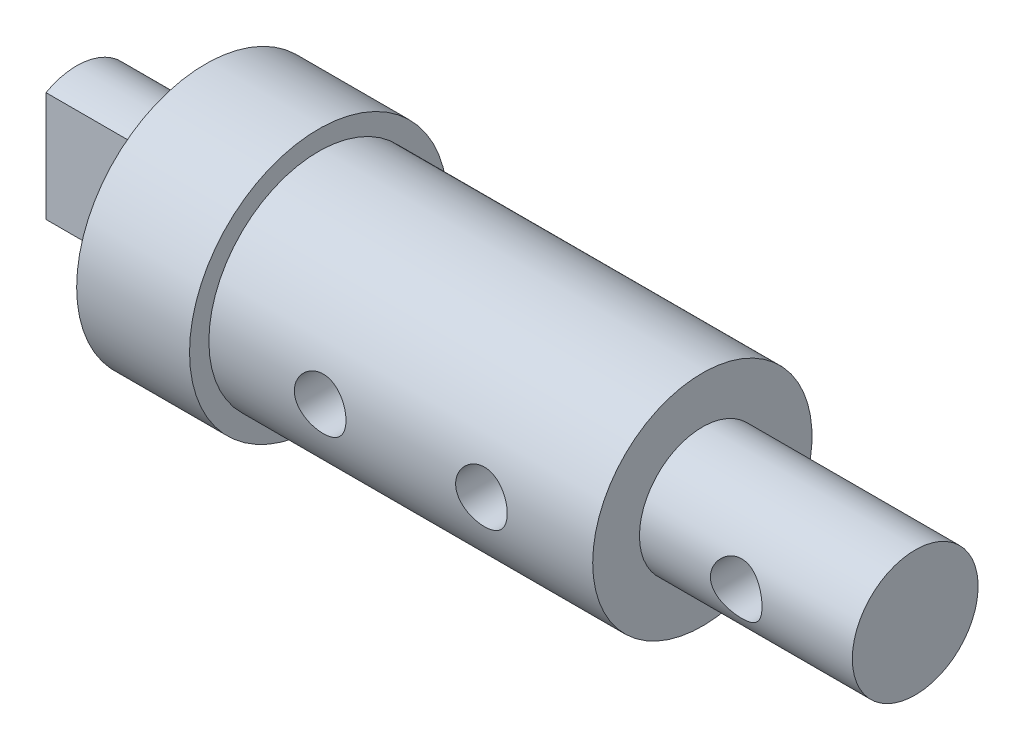
SolidWorks part; units mm, degrees
material "Nylon 101"
ref_plane "Front Plane" through (0, 0, 0) normal (0, 0, 1) x (1, 0, 0)
ref_plane "Top Plane" through (0, 0, 0) normal (0, 1, 0) x (1, 0, 0)
ref_plane "Right Plane" through (0, 0, 0) normal (1, 0, 0) x (0, 0, -1)
sketch "Sketch1" plane through (0, 0, 0) normal (0, 0, 1) x (1, 0, 0)
  line L0 (-11, 0) -> (11, 0)
  line L1 (11, 0) -> (11, 1.95)
  line L2 (11, 1.95) -> (4.4, 1.95)
  line L3 (4.4, 1.95) -> (4.4, 3.4)
  line L4 (0, 0) -> (49607.6871, 0) construction
  line L5 (4.4, 3.4) -> (-7.5, 3.4)
  line L6 (-7.5, 3.4) -> (-7.5, 4)
  line L7 (-7.5, 4) -> (-11, 4)
  line L8 (-11, 4) -> (-11, 0)
  point P4 (0, 0)
  dimension "D1" = 6.8
  dimension "D2" = 3.9
  dimension "D3" = 6.6
  dimension "D4" = 3.5
  dimension "D5" = 22
  dimension "D6" = 8
revolve "Revolve1" add sketch "Sketch1" angle 360 about L4
ref_plane "Plane1" through (0, 0, 3.4) normal (0, 0, 1) x (1, 0, 0)
sketch "Sketch2" plane through (0, 0, 3.4) normal (0, 0, 1) x (1, 0, 0)
  line L0 (-7.5, 0) -> (-4.05, 0) construction
  line L1 (-4.05, 0) -> (0.95, 0) construction
  line L2 (0.95, 0) -> (4.4, 0) construction
  line L3 (4.4, -3.4) -> (4.4, 3.4) construction
  line L4 (-7.5, -3.4) -> (-7.5, 3.4) construction
  dimension "D1" = 5
hole_wizard "M2x0.4 Tapped Hole1" positions "Sketch3" profile "Sketch5" tap size "M2x0.4" standard "ANSI Metric" end condition through all
sketch "Sketch3" plane through (0, 0, 3.4) normal (0, 0, 1) x (1, 0, 0)
  point P0 (-4.05, 0)
  point P3 (0.95, 0)
cosmetic thread "Hole Thread1" parameters "D2"=2
cosmetic thread "Hole Thread2" parameters "D2"=2
sketch "Sketch5" plane through (-4.05, 0, 3.4) normal (1, 0, 0) x (0, -1, 0)
  line L0 (0, 0) -> (0, 7.4)
  line L1 (0, 7.4) -> (0.8, 7.4)
  line L2 (0.8, 7.4) -> (0.8, 0)
  line L5 (0.8, 0) -> (0, 0)
  line L11 (0, -6.35) -> (0, 107.95) construction
  dimension "Thru Tap Drill Dia." = 1.6
  dimension "Thru Tap Drill Depth" = 7.4
sketch "Sketch6" plane through (-11, 0, 0) normal (-1, 0, 0) x (0, 0, 1)
  line L0 (1, 1.7321) -> (1, -1.7321) construction
  line L1 (0.95, 1.7029) -> (0.95, -1.7029)
  arc A0 (1, 1.7321) -> (1, -1.7321) centre (0, 0) ccw construction
  arc A1 (0.95, 1.7029) -> (0.95, -1.7029) centre (0, 0) ccw
  dimension "D1" = 4
  dimension "D2" = 1
  dimension "D3" = 0.05
extrude "Boss-Extrude1" add sketch "Sketch6" along normal blind 4
hole_wizard "M2x0.4 Tapped Hole2" positions "Sketch7" profile "Sketch8" tap size "M2x0.4" standard "ANSI Metric"
sketch "Sketch7" plane through (0, 0, 3.4) normal (0, 0, 1) x (1, 0, 0)
  line L0 (7.4, 0) -> (4.4, 0) construction
  line L2 (4.4, -3.4) -> (4.4, 3.4) construction
  point P0 (7.4, 0)
  dimension "D1" = 3
sketch "Sketch8" plane through (7.4, 0, 3.4) normal (1, 0, 0) x (0, -1, 0)
  line L0 (0, 0) -> (0, 3.4807)
  line L1 (0, 3.4807) -> (0.8, 3)
  line L2 (0.8, 3) -> (0.8, 0.225)
  line L3 (0.8, 0.225) -> (1.025, 0)
  line L5 (1.025, 0) -> (0, 0)
  line L6 (-0.8, 0.225) -> (-1.025, 0) construction
  line L10 (0, 3.4807) -> (-0.8, 3) construction
  line L11 (0, -6.35) -> (0, 107.95) construction
  dimension "Tap Drill Dia." = 1.6
  dimension "Tap Drill Depth" = 3
  dimension "Near C'Sink Dia." = 2.05
  dimension "Near C'Sink Angle" = 90
  dimension "Drill Angle" = 118
cosmetic thread "Hole Thread3" parameters "D1"=3, "D2"=2
hole_wizard "Hole5" positions "Sketch12" profile "Sketch13" legacy
sketch "Sketch12" plane through (-15, 0, 0) normal (-1, 0, 0) x (0, 0, 1)
  point P0 (0, 0)
sketch "Sketch13" plane through (-15, 0, 0) normal (0, 1, 0) x (0, 0, 1)
  line L0 (0, 0) -> (0, 5)
  line L1 (0, 5) -> (0.9, 5)
  line L2 (0.9, 5) -> (0.9, 0)
  line L3 (0.9, 0) -> (0, 0)
  line L4 (0, 110) -> (0, -10) construction
  dimension "Diameter" = 1.8
  dimension "Depth" = 5
